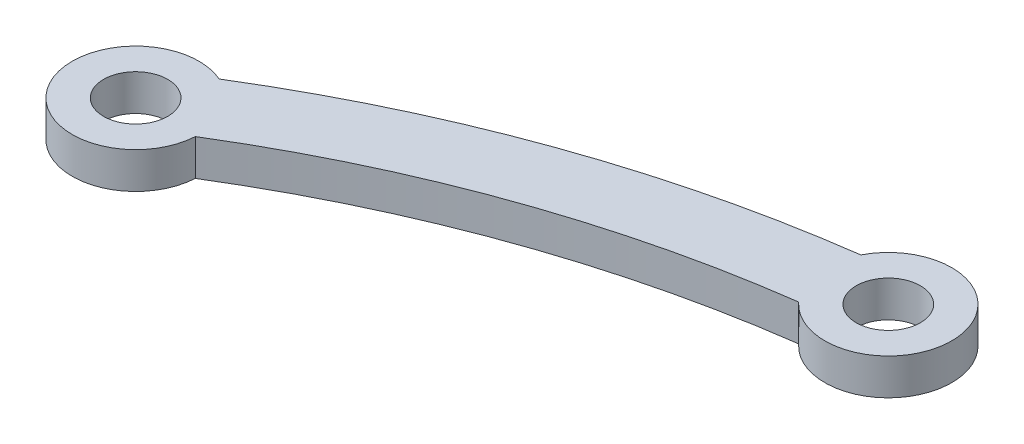
SolidWorks part; units mm, degrees
ref_plane "Front Plane" through (0, 0, 0) normal (0, 0, 1) x (1, 0, 0)
ref_plane "Top Plane" through (0, 0, 0) normal (0, 1, 0) x (1, 0, 0)
ref_plane "Right Plane" through (0, 0, 0) normal (1, 0, 0) x (0, 0, -1)
sketch "Sketch1" plane through (0, 0, 0) normal (0, 1, 0) x (1, 0, 0)
  line L0 (-65.3633, 0) -> (47.0746, 0) construction
  line L1 (2.7079, 20.2631) -> (-8.3301, 26.5443) construction
  line L2 (-8.3301, 26.5443) -> (-47.214, 12.7) construction
  line L3 (-47.214, 12.7) -> (-47.214, -12.7) construction
  line L4 (-47.214, 0) -> (-78.4896, 0) construction
  line L5 (2.7079, -20.2631) -> (-8.3301, -26.5443) construction
  line L6 (-8.3301, -26.5443) -> (-47.214, -12.7) construction
  line L7 (2.7079, 20.2631) -> (2.6537, 20.1678) construction
  line L8 (2.7079, -20.2631) -> (2.6537, -20.1678) construction
  line L9 (-9.821, 30.7318) -> (-48.705, 16.8875) construction
  line L10 (-26.4089, -2.7134) -> (-47.214, -2.7134)
  line L11 (-26.4089, -2.7134) -> (-26.4089, 2.7134)
  line L12 (-26.4089, 2.7134) -> (-47.214, 2.7134)
  line L13 (-47.214, -2.7134) -> (-47.214, 2.7134)
  line L14 (-26.4089, -2.7134) -> (-47.214, 2.7134) construction
  line L15 (-26.4089, 2.7134) -> (-47.214, -2.7134) construction
  line L16 (-6.8392, 22.3568) -> (-45.7231, 8.5125) construction
  arc A0 (2.7079, 20.2631) -> (50.8693, 36.4224) centre (35.8219, 1.4197) cw construction
  arc A1 (2.7079, -20.2631) -> (50.8693, -36.4224) centre (35.8219, -1.4197) ccw construction
  circle A2 centre (8.89, 0) radius 6.35 construction
  circle A3 centre (15.24, 0) radius 12.7 construction
  arc A5 (-48.705, 16.8875) -> (-45.7231, 8.5125) centre (-47.214, 12.7) ccw
  arc A6 (-9.821, 30.7318) -> (-6.8392, 22.3568) centre (-8.3301, 26.5443) cw
  circle A7 centre (-47.214, 12.7) radius 2.2479
  circle A8 centre (-8.3301, 26.5443) radius 2.2479
  arc A11 (-45.4322, 16.7722) -> (-42.7765, 12.4417) centre (-47.214, 12.7) ccw
  arc A12 (-11.6059, 23.5397) -> (-12.2845, 28.5742) centre (-8.3301, 26.5443) ccw
  arc A14 (-45.4322, 16.7722) -> (-12.2845, 28.5742) centre (-0.9063, -55.8349) cw
  arc A15 (-42.7765, 12.4417) -> (-11.6059, 23.5397) centre (-0.9063, -55.8349) cw
  point P25 (-36.8115, 0)
  dimension "D1" = 38.1
  dimension "D7" = 25.4
  dimension "D8" = 12.7
  dimension "D11" = 4.4958
  dimension "D12" = 5.08
  dimension "D2" = 12.7
  dimension "D3" = 41.275
  dimension "D4" = 50.8
  dimension "D5" = 90
  dimension "D6" = 25.4
  dimension "D9" = 4.445
  dimension "D10" = 4.445
extrude "Boss-Extrude1" add sketch "Sketch1" along normal blind 2.54
